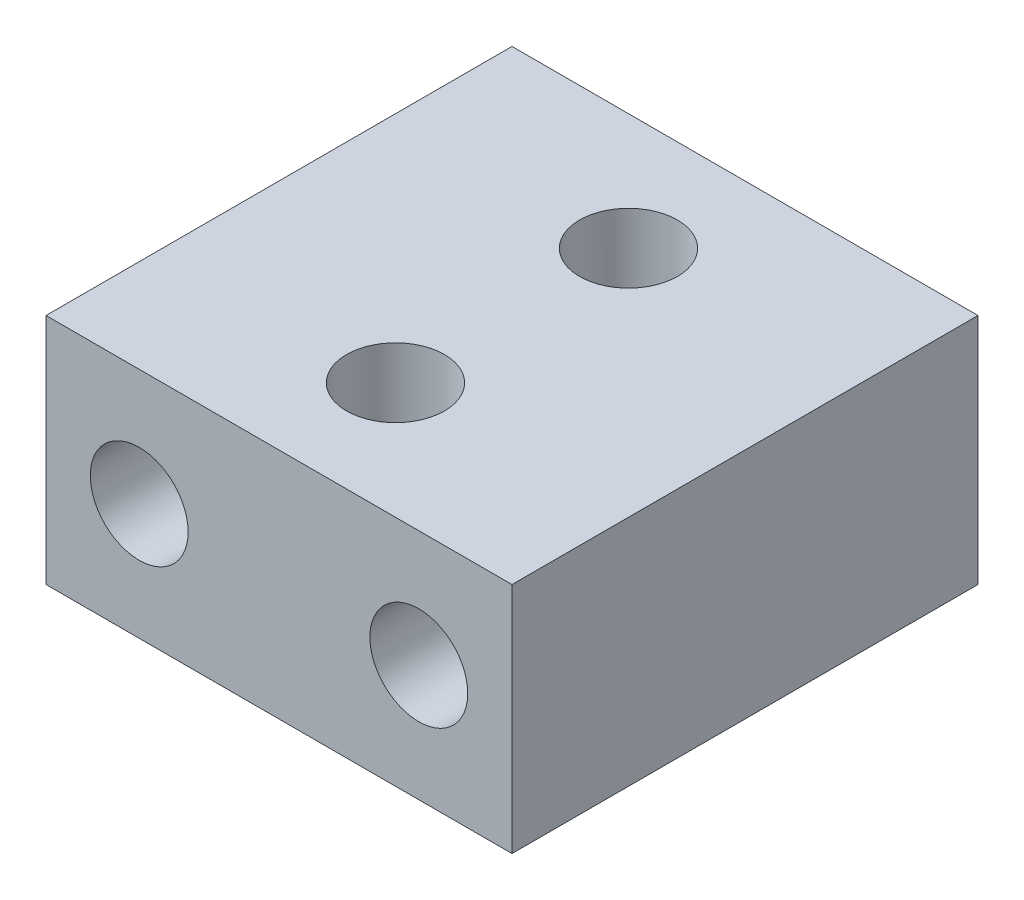
SolidWorks part; units mm, degrees
ref_plane "Front Plane" through (0, 0, 0) normal (0, 0, 1) x (1, 0, 0)
ref_plane "Top Plane" through (0, 0, 0) normal (0, 1, 0) x (1, 0, 0)
ref_plane "Right Plane" through (0, 0, 0) normal (1, 0, 0) x (0, 0, -1)
sketch "Sketch1" plane through (0, 0, 0) normal (0, 0, 1) x (1, 0, 0)
  line L1 (0, 0) -> (20, 0)
  line L2 (0, 0) -> (0, 10)
  line L3 (0, 10) -> (20, 10)
  line L4 (20, 0) -> (20, 10)
  circle A0 centre (4, 5) radius 2.1
  circle A1 centre (16, 5) radius 2.1
  dimension "D1" = 4.2
  dimension "D2" = 10
  dimension "D3" = 20
  dimension "D4" = 5
  dimension "D5" = 4
  dimension "D6" = 4
extrude "Boss-Extrude1" add sketch "Sketch1" along normal blind 20
sketch "Sketch2" plane through (0, 0, 0) normal (0, -1, 0) x (1, 0, 0)
  line L0 (0, 20) -> (20, 20) construction
  line L1 (0, 0) -> (20, 0) construction
  line L2 (0, 20) -> (0, 0) construction
  circle A0 centre (10, 15) radius 2.1
  circle A1 centre (10, 5) radius 2.1
  dimension "D1" = 5
  dimension "D4" = 4.2
  dimension "D2" = 5
  dimension "D3" = 10
extrude "Cut-Extrude1" cut sketch "Sketch2" against normal blind 30
